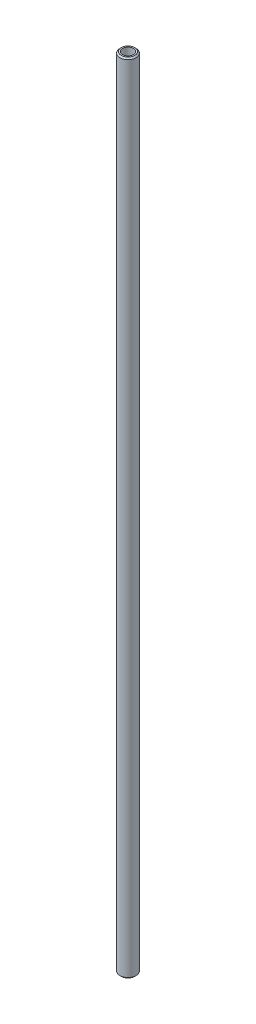
SolidWorks part; units mm, degrees
ref_plane "Plan de face" through (0, 0, 0) normal (0, 0, 1) x (1, 0, 0)
ref_plane "Plan de dessus" through (0, 0, 0) normal (0, 1, 0) x (1, 0, 0)
ref_plane "Plan de droite" through (0, 0, 0) normal (1, 0, 0) x (0, 0, -1)
sketch "Esquisse2" plane through (0, 0, 0) normal (0, 1, 0) x (1, 0, 0)
  line L0 (5612.1083, -596.9248) -> (5644.5772, -595.5028) construction
  circle A0 centre (5628.3428, -596.2138) radius 3
  circle A1 centre (5628.3428, -596.2138) radius 2
  dimension "D1" = 6
  dimension "D2" = 4
extrude "Boss.-Extru.1" add sketch "Esquisse2" along normal blind 295
chamfer "Chanfrein1" distance 0.5 angle 45 2 edges at (5628.3428, 295, 599.2138) (5628.3428, 0, 599.2138)
